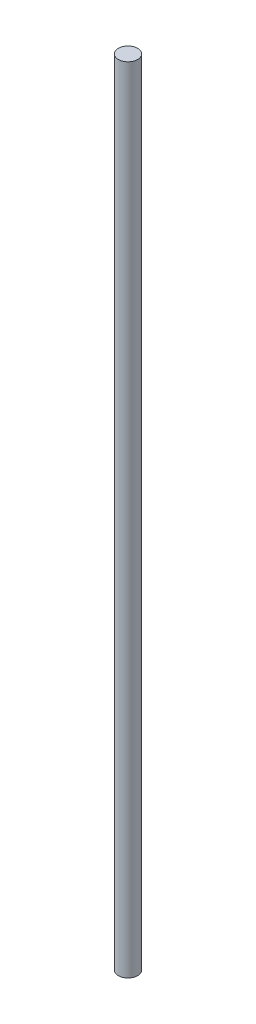
SolidWorks part; units mm, degrees
ref_plane "Front Plane" through (0, 0, 0) normal (0, 0, 1) x (1, 0, 0)
ref_plane "Top Plane" through (0, 0, 0) normal (0, 1, 0) x (1, 0, 0)
ref_plane "Right Plane" through (0, 0, 0) normal (1, 0, 0) x (0, 0, -1)
sketch "Sketch1" plane through (0, 0, 0) normal (0, 1, 0) x (1, 0, 0)
  circle A0 centre (0, 0) radius 2.5
  dimension "D1" = 5
extrude "Boss-Extrude1" add sketch "Sketch1" along normal blind 205
